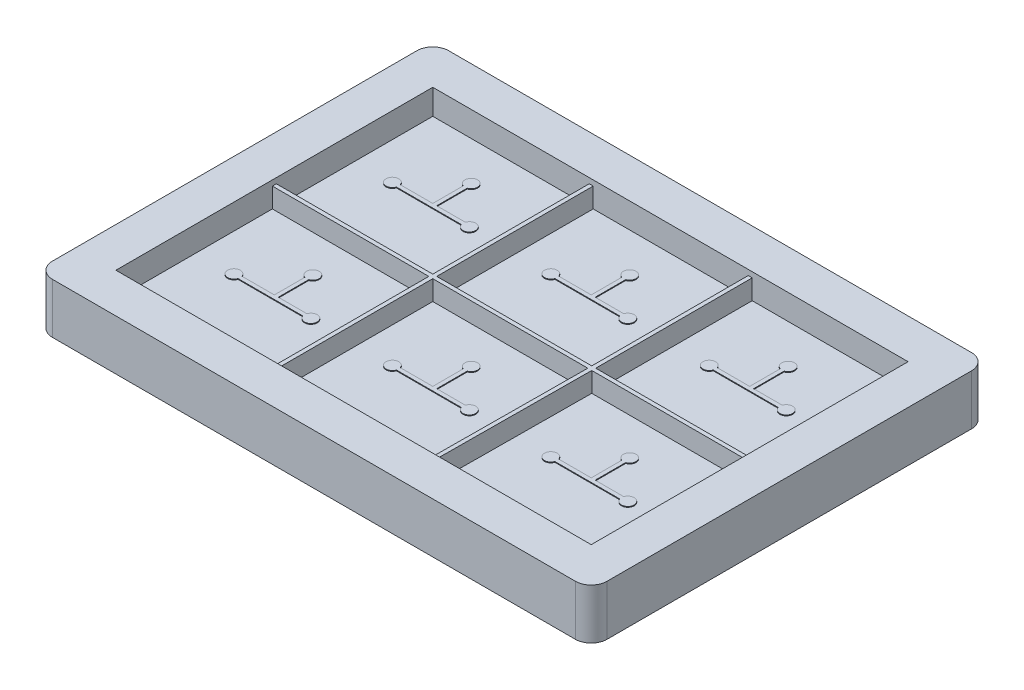
SolidWorks part; units mm, degrees
ref_plane "Front Plane" through (0, 0, 0) normal (0, 0, 1) x (1, 0, 0)
ref_plane "Top Plane" through (0, 0, 0) normal (0, 1, 0) x (1, 0, 0)
ref_plane "Right Plane" through (0, 0, 0) normal (1, 0, 0) x (0, 0, -1)
sketch "Sketch1" plane through (0, 0, 0) normal (0, 1, 0) x (1, 0, 0)
  line L1 (-35, 25) -> (35, 25)
  line L2 (-35, 25) -> (-35, -25)
  line L3 (-35, -25) -> (35, -25)
  line L4 (35, 25) -> (35, -25)
  line L5 (-35, 25) -> (35, -25) construction
  line L6 (-35, -25) -> (35, 25) construction
  point P0 (0, 0)
  dimension "D1" = 70
  dimension "D2" = 50
extrude "Boss-Extrude1" add sketch "Sketch1" along normal blind 6.35
sketch "Sketch2" plane through (0, 6.35, 0) normal (0, 1, 0) x (1, 0, 0)
  line L5 (30, -20) -> (30, 20)
  line L6 (30, -20) -> (30, 20)
  line L11 (30, 20) -> (-30, 20)
  line L12 (-30, 20) -> (-30, -20)
  line L13 (-30, -20) -> (30, -20)
  line L15 (30, 20) -> (-30, 20)
  line L16 (-30, 20) -> (-30, -20)
  line L17 (-30, -20) -> (30, -20)
  dimension "D1" = 5
extrude "Cut-Extrude1" cut sketch "Sketch2" against normal blind 3.175
sketch "Sketch10" plane through (0, 3.175, 0) normal (0, 1, 0) x (1, 0, 0)
  line L0 (-10.25, -0.25) -> (-10.25, -20)
  line L2 (-30, 0.25) -> (-10.25, 0.25)
  line L3 (-30, 0.25) -> (-30, -0.25)
  line L4 (-30, -0.25) -> (-10.25, -0.25)
  line L5 (30, 0.25) -> (30, -0.25)
  line L6 (-30, 0.25) -> (30, -0.25) construction
  line L7 (-30, -0.25) -> (30, 0.25) construction
  line L9 (-10.25, 20) -> (-9.75, 20)
  line L10 (-10.25, 20) -> (-10.25, 0.25)
  line L11 (-10.25, -20) -> (-9.75, -20)
  line L12 (-9.75, 20) -> (-9.75, 0.25)
  line L13 (-10.25, 20) -> (-9.75, -20) construction
  line L14 (-10.25, -20) -> (-9.75, 20) construction
  line L15 (9.8186, 20) -> (10.3186, 20)
  line L16 (9.8186, 20) -> (9.8186, 0.25)
  line L17 (9.6814, -20) -> (10.1814, -20)
  line L18 (10.3186, 20) -> (10.3186, 0.25)
  line L19 (9.8186, 20) -> (10.1814, -20) construction
  line L20 (9.6814, -20) -> (10.3186, 20) construction
  line L22 (-9.75, 0.25) -> (9.8186, 0.25)
  line L24 (-9.75, -0.25) -> (-9.75, -20)
  line L25 (-9.75, -0.25) -> (9.8186, -0.25)
  line L26 (-30, 20) -> (-30, -20) construction
  line L27 (30, -20) -> (30, 20) construction
  line L28 (10.3186, 0.25) -> (30, 0.25)
  line L29 (30, 20) -> (-30, 20) construction
  line L30 (10.3186, -0.25) -> (10.1814, -20)
  line L31 (10.3186, -0.25) -> (30, -0.25)
  line L33 (9.8186, -0.25) -> (9.6814, -20)
  point P0 (0, 0)
  point P1 (0, 0)
  point P6 (-10, 0)
  point P11 (10, 0)
  point P13 (-10, 0)
  point P18 (10, 0)
  dimension "D1" = 20
  dimension "D2" = 20
  dimension "D3" = 0.5
extrude "Dividers" add sketch "Sketch10" along normal blind 2.5
sketch "Sketch11" plane through (0, 3.175, 0) normal (0, 1, 0) x (1, 0, 0)
  line L0 (-20.375, 9.875) -> (-19.875, 9.875)
  line L1 (-24.4649, 10.375) -> (-16.2665, 10.375)
  line L2 (-24.4649, 10.375) -> (-24.4649, 9.875)
  line L3 (-24.4649, 9.875) -> (-16.2665, 9.875)
  line L4 (-16.2665, 10.375) -> (-16.2665, 9.875)
  line L5 (-16.2665, 10.375) -> (-16.2665, 9.875)
  line L6 (-20.375, 14.2242) -> (-19.875, 14.2242)
  line L7 (-20.375, 14.2242) -> (-20.375, 9.875)
  line L9 (-19.875, 14.2242) -> (-19.875, 9.875)
  line L10 (-30, 20) -> (-10.25, 20) construction
  line L11 (-24.4649, 9.875) -> (-24.4649, 10.375)
  line L12 (-10.25, 20) -> (-10.25, 0.25) construction
  line L13 (-10.25, 20) -> (-10.25, 0.25) construction
  arc A0 (-24.4649, 10.375) -> (-24.4649, 9.875) centre (-25.2248, 10.125) ccw
  arc A1 (-16.2665, 9.875) -> (-16.2665, 10.375) centre (-15.5065, 10.125) ccw
  arc A2 (-20.375, 14.2242) -> (-19.875, 14.2242) centre (-20.125, 14.9841) cw
  point P1 (-20.125, 9.875)
  point P5 (-20.125, 20)
  point P17 (-10.25, 10.125)
  point P23 (0, 0)
  dimension "D1" = 0.8
  dimension "D3" = 0.5
extrude "Boss-Extrude3" add sketch "Sketch11" along normal blind 0.1 contours L2 A0 | L7 L1 L2 L3 | L9 L6 L7 L1 | L1 L9 L3 L4 | L4 A1 | A2 L6
pattern_linear "LPattern1" count 3 spacing 20 along (1, 0, 0) count 2 spacing 20 along (0, 0, 1) of "Boss-Extrude3"
fillet "Fillet1" radius 2 4 edges at (-35, 3.175, -25) (35, 3.175, -25) (35, 3.175, 25) (-35, 3.175, 25)
equation "\"2.5mmm\"=2"
